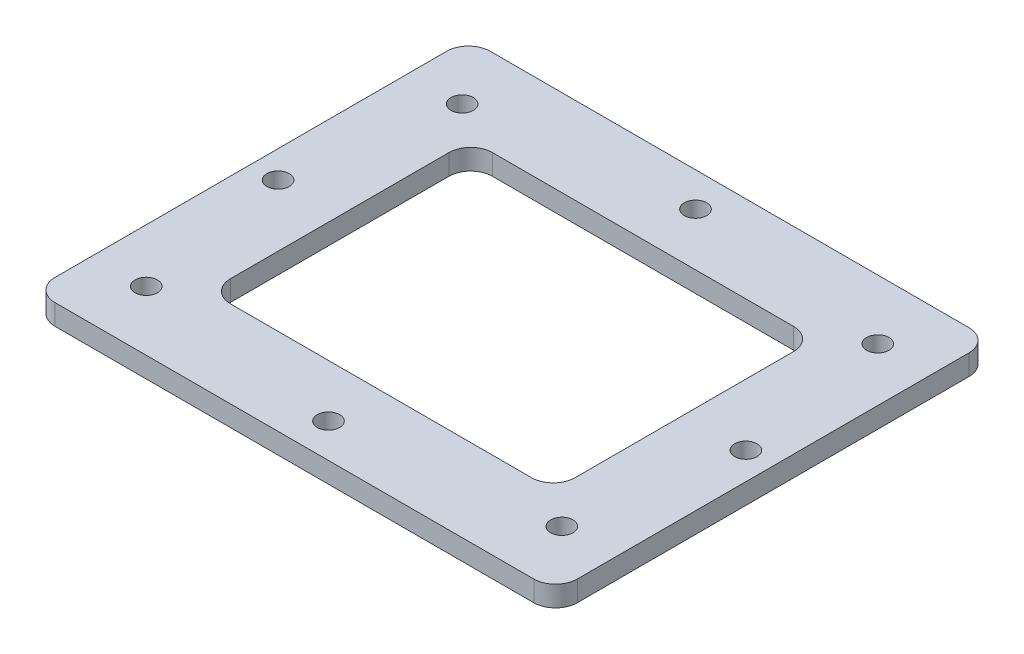
SolidWorks part; units mm, degrees
ref_plane "Front Plane" through (0, 0, 0) normal (0, 0, 1) x (1, 0, 0)
ref_plane "Top Plane" through (0, 0, 0) normal (0, 1, 0) x (1, 0, 0)
ref_plane "Right Plane" through (0, 0, 0) normal (1, 0, 0) x (0, 0, -1)
sketch "Sketch1" plane through (0, 0, 0) normal (0, 1, 0) x (1, 0, 0)
  line L0 (0, 0) -> (0, 26.77) construction
  line L5 (-38.1, 31.75) -> (38.1, 31.75)
  line L6 (-38.1, 31.75) -> (-38.1, -31.75)
  line L7 (-38.1, -31.75) -> (38.1, -31.75)
  line L8 (38.1, 31.75) -> (38.1, -31.75)
  line L9 (-38.1, 31.75) -> (38.1, -31.75) construction
  line L10 (-38.1, -31.75) -> (38.1, 31.75) construction
  line L11 (-30.315, 23.045) -> (30.315, 23.045) construction
  line L12 (-30.315, 23.045) -> (-30.315, -23.045) construction
  line L13 (-30.315, -23.045) -> (30.315, -23.045) construction
  line L14 (30.315, 23.045) -> (30.315, -23.045) construction
  line L15 (-30.315, 23.045) -> (30.315, -23.045) construction
  line L16 (-30.315, -23.045) -> (30.315, 23.045) construction
  line L17 (0, 0) -> (34.125, 0) construction
  line L18 (0, 0) -> (0, -26.77) construction
  line L19 (0, 0) -> (-34.125, 0) construction
  line L21 (-25.1404, 19.1114) -> (25.1404, 19.1114)
  line L22 (-25.1404, 19.1114) -> (-25.1404, -19.1114)
  line L23 (-25.1404, -19.1114) -> (25.1404, -19.1114)
  line L24 (25.1404, 19.1114) -> (25.1404, -19.1114)
  line L25 (-25.1404, 19.1114) -> (25.1404, -19.1114) construction
  line L26 (-25.1404, -19.1114) -> (25.1404, 19.1114) construction
  point P0 (0, 0)
  point P7 (0, 0)
  point P13 (-30.315, 23.045)
  point P14 (30.315, 23.045)
  point P15 (30.315, -23.045)
  point P16 (-30.315, -23.045)
  point P22 (0, 26.77)
  point P23 (-34.125, 0)
  point P24 (0, -26.77)
  point P25 (34.125, 0)
  dimension "D1" = 63.5
  dimension "D2" = 76.2
  dimension "D3" = 60.63
  dimension "D4" = 46.09
  dimension "D5" = 53.54
  dimension "D6" = 68.25
  dimension "D7" = 6.5
extrude "Boss-Extrude1" add sketch "Sketch1" along normal mid plane 3
fillet "Fillet1" radius 3.175 8 edges at (-38.1, 0, -31.75) (38.1, 0, -31.75) (38.1, 0, 31.75) (-38.1, 0, 31.75) (-25.1404, 0, 19.1114) (25.1404, 0, 19.1114) (25.1404, 0, -19.1114) (-25.1404, 0, -19.1114)
sketch "Sketch2" plane through (0, 1.5, 0) normal (0, 1, 0) x (1, 0, 0)
  point P0 (-34.125, 0)
  point P1 (-30.315, -23.045)
  point P3 (0, -26.77)
  point P5 (30.315, -23.045)
  point P7 (34.125, 0)
  point P9 (30.315, 23.045)
  point P11 (0, 26.77)
  point P13 (-30.315, 23.045)
hole_wizard "#4 Clearance Hole1" positions "Sketch2" profile "Sketch3" hole size "#4" standard "ANSI Inch"
sketch "Sketch3" plane through (-34.125, 1.5, 0) normal (1, 0, 0) x (0, 0, 1)
  line L0 (0, 0) -> (0, 7.6)
  line L1 (0, 7.6) -> (1.6319, 6.6194)
  line L2 (1.6319, 6.6194) -> (1.6319, 0)
  line L5 (1.6319, 0) -> (0, 0)
  line L10 (0, 7.6) -> (-1.632, 6.6194) construction
  line L11 (0, -6.35) -> (0, 107.95) construction
  dimension "Hole Dia." = 3.2639
  dimension "Hole Depth" = 7.6
  dimension "Drill Angle" = 118
